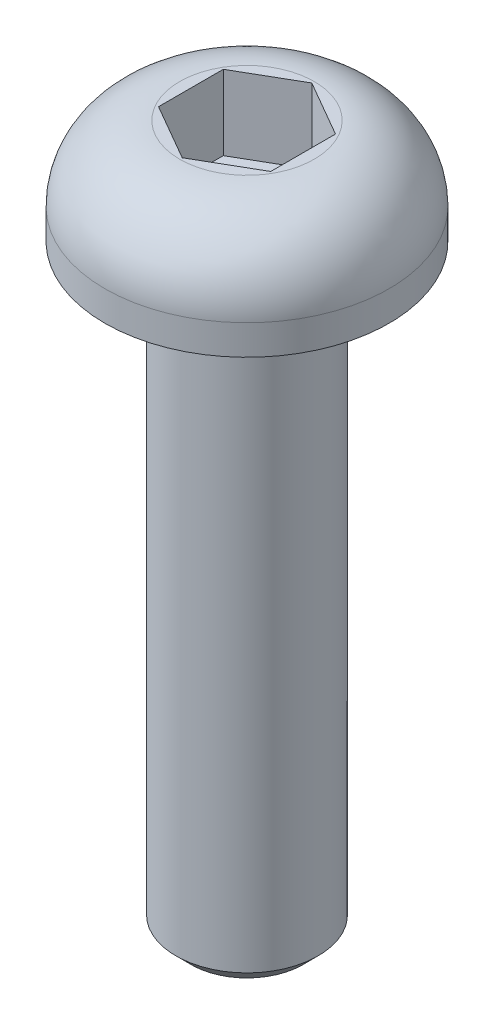
SolidWorks part; units mm, degrees
material "铸造合金钢"
ref_plane "前视基准面" through (0, 0, 0) normal (0, 0, 1) x (1, 0, 0)
ref_plane "上视基准面" through (0, 0, 0) normal (0, 1, 0) x (1, 0, 0)
ref_plane "右视基准面" through (0, 0, 0) normal (1, 0, 0) x (0, 0, -1)
sketch "草图1" plane through (0, 0, 0) normal (0, 1, 0) x (1, 0, 0)
  circle A0 centre (0, 0) radius 1.9
  dimension "D1" = 3.8
extrude "凸台-拉伸1" add sketch "草图1" along normal blind 1.4
sketch "草图2" plane through (0, 1.4, 0) normal (0, 1, 0) x (1, 0, 0)
  line L1 (0, -0.866) -> (0.75, -0.433)
  line L2 (0.75, -0.433) -> (0.75, 0.433)
  line L3 (0.75, 0.433) -> (0, 0.866)
  line L4 (0, 0.866) -> (-0.75, 0.433)
  line L5 (-0.75, 0.433) -> (-0.75, -0.433)
  line L6 (-0.75, -0.433) -> (0, -0.866)
  circle A0 centre (0, 0) radius 0.75 construction
  dimension "D1" = 1.5
extrude "切除-拉伸1" cut sketch "草图2" against normal blind 1
fillet "圆角1" radius 1 1 edges at (0, 1.4, 1.9)
sketch "草图3" plane through (0, 0, 0) normal (0, -1, 0) x (1, 0, 0)
  circle A0 centre (0, 0) radius 0.95
  dimension "D1" = 1.9
extrude "凸台-拉伸2" add sketch "草图3" along normal blind 8
chamfer "倒角1" distance 0.2 angle 45 1 edges at (0, -8, -0.95)
